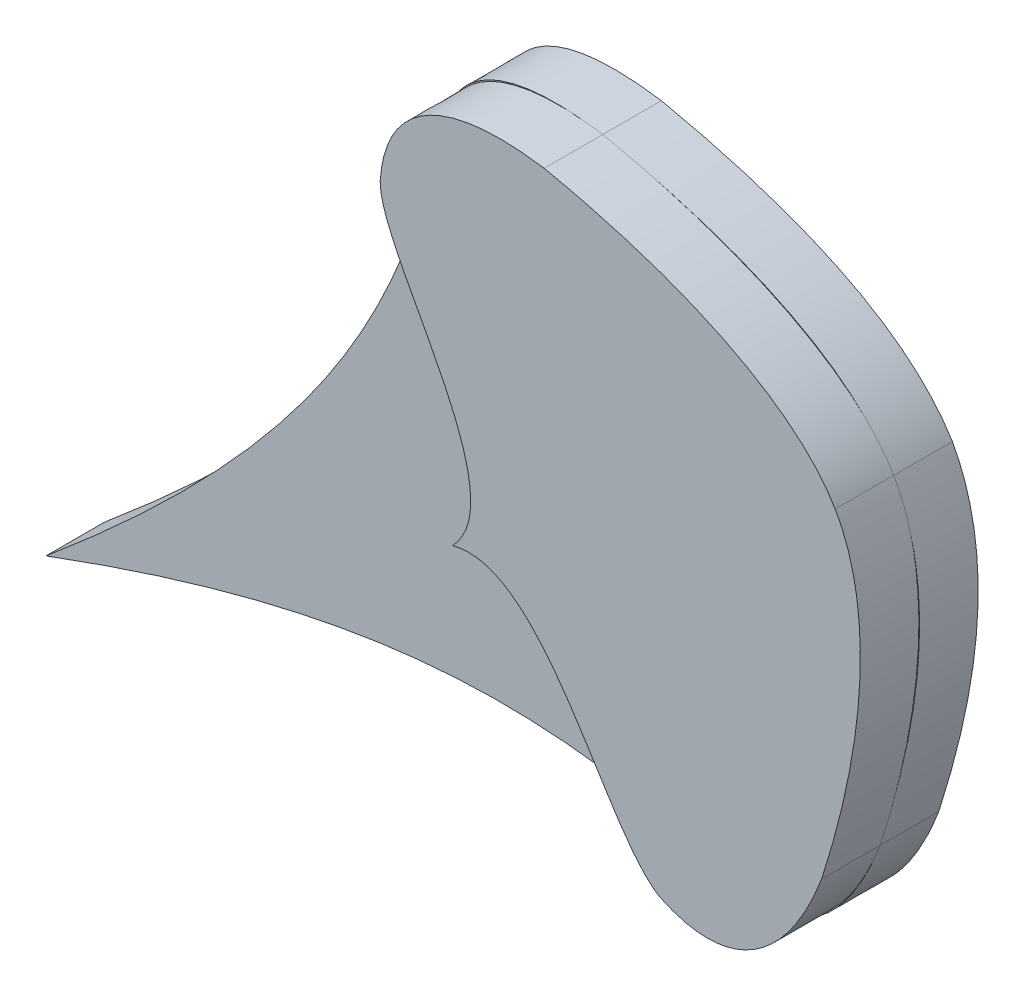
SolidWorks part; units mm, degrees
ref_plane "Front Plane" through (0, 0, 0) normal (0, 0, 1) x (1, 0, 0)
ref_plane "Top Plane" through (0, 0, 0) normal (0, 1, 0) x (1, 0, 0)
ref_plane "Right Plane" through (0, 0, 0) normal (1, 0, 0) x (0, 0, -1)
sketch "Sketch1" plane through (0, 0, 0) normal (0, 0, 1) x (1, 0, 0)
  line L0 (318.6667, 759.5) -> (1593.3333, 759.5) construction
  line L1 (1662.7369, 1175.7643) -> (205.3165, 327.0421) construction
  spline S0 degree 2 poles (1087.1878, 840.5959) (1076.6791, 857.8748) (1037.5166, 866.14) knots 0 0 0 1 1 1
  spline S1 degree 2 poles (1037.5166, 866.14) (1011.2956, 870.0662) (1009.5256, 850.301) knots 0 0 0 1 1 1
  spline S2 degree 3 poles (1009.5256, 850.301) (1001.9073, 820.6702) (988.2064, 794.7091) (942.4827, 756.3275) knots 0 0 0 0 1 1 1 1
  spline S3 degree 3 poles (1057.3016, 768.2604) (1027.7708, 776.2576) (998.4299, 777.1535) (942.4827, 756.3275) knots 0 0 0 0 1 1 1 1
  spline S4 degree 2 poles (1084.8913, 784.7886) (1075.3657, 760.0455) (1057.3016, 768.2604) knots 0 0 0 1 1 1
  spline S5 degree 2 poles (1087.1878, 840.5959) (1097.0298, 822.9287) (1084.8913, 784.7886) knots 0 0 0 1 1 1
extrude "Boss-Extrude1" add sketch "Sketch1" along normal blind 10
sketch "Sketch3" plane through (0, 0, 10) normal (0, 0, 1) x (1, 0, 0)
  line L0 (1087.1878, 840.5959) -> (942.4827, 756.3275) construction
  spline S0 degree 3 poles (1087.1878, 840.5959) (1081.4871, 850.5298) (1065.2325, 860.337) (1037.5166, 866.14) knots 0 0 0 0 1 1 1 1
  spline S1 degree 3 poles (1037.5166, 866.14) (1020.0044, 868.8136) (1010.348, 862.5879) (1009.5256, 850.301) knots 0 0 0 0 1 1 1 1
  spline S2 degree 3 poles (1009.5256, 850.301) (1009.3553, 839.6055) (1033.3615, 814.3022) (1021.8634, 802.5545) knots 0 0 0 0 1 1 1 1
  spline S3 degree 3 poles (1087.1878, 840.5959) (1093.0144, 830.7353) (1093.5222, 811.758) (1084.8913, 784.7886) knots 0 0 0 0 1 1 1 1
  spline S4 degree 3 poles (1084.8913, 784.7886) (1078.5741, 768.2381) (1068.3938, 762.9119) (1057.3016, 768.2604) knots 0 0 0 0 1 1 1 1
  spline S5 degree 3 poles (1057.3016, 768.2604) (1047.9152, 773.3907) (1037.7553, 806.7573) (1021.8634, 802.5545) knots 0 0 0 0 1 1 1 1
extrude "Boss-Extrude2" add sketch "Sketch3" along normal blind 10
